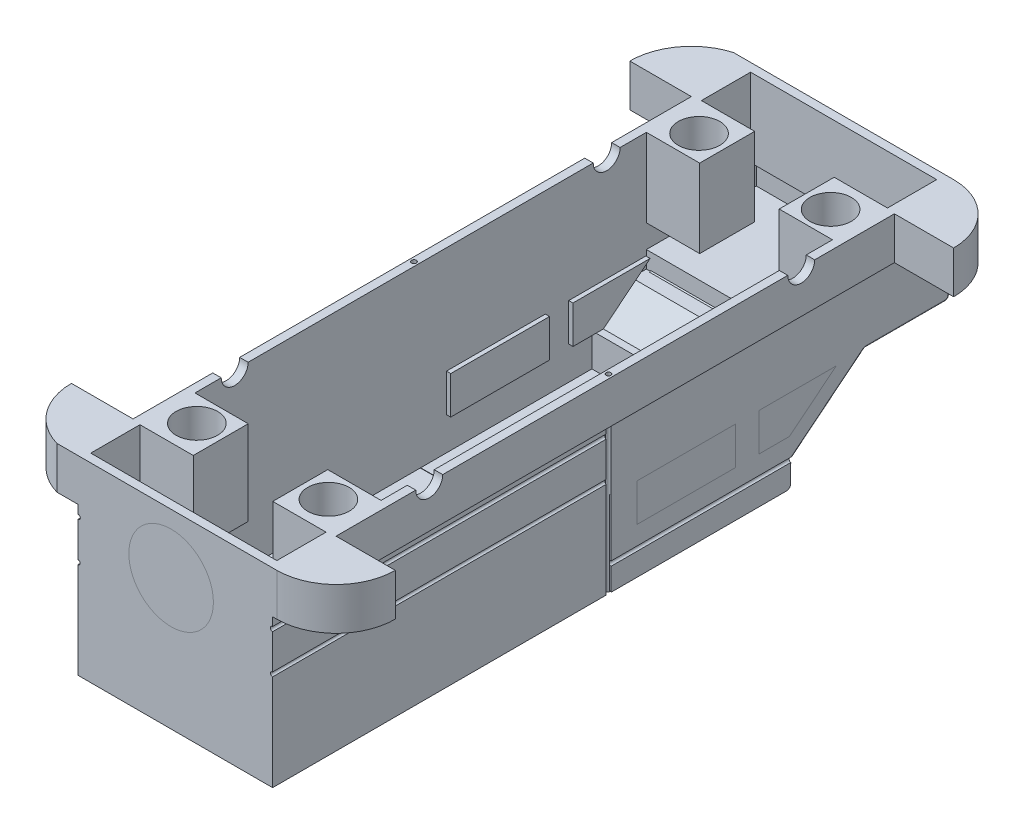
SolidWorks part; units mm, degrees
ref_plane "Front Plane" through (0, 0, 0) normal (0, 0, 1) x (1, 0, 0)
ref_plane "Top Plane" through (0, 0, 0) normal (0, 1, 0) x (1, 0, 0)
ref_plane "Right Plane" through (0, 0, 0) normal (1, 0, 0) x (0, 0, -1)
sketch "Sketch1" plane through (0, 0, 0) normal (0, 1, 0) x (1, 0, 0)
  line L1 (-24.8944, 17.78) -> (41.1456, 17.78)
  line L2 (-19.8144, 0) -> (-19.8144, -167.64)
  line L3 (-24.8944, -185.42) -> (41.1456, -185.42)
  line L4 (41.1456, 0) -> (41.1456, -167.64)
  line L5 (58.9256, 0) -> (41.1456, 0)
  line L6 (-38.3059, -167.64) -> (-19.8144, -167.64)
  line L7 (-38.3059, 0) -> (-19.8144, 0)
  line L8 (58.9256, -167.64) -> (41.1456, -167.64)
  arc A0 (58.9256, 0) -> (41.1456, 17.78) centre (41.1456, 0) ccw
  arc A1 (-38.3059, 0) -> (-24.8944, 17.78) centre (-19.8144, 0) cw
  arc A2 (-38.3059, -167.64) -> (-24.8944, -185.42) centre (-19.8144, -167.64) ccw
  arc A3 (58.9256, -167.64) -> (41.1456, -185.42) centre (41.1456, -167.64) cw
  dimension "D1" = 66.04
  dimension "D2" = 203.2
  dimension "D3" = 60.96
  dimension "0.8" = 17.78
extrude "Boss-Extrude1" add sketch "Sketch1" along normal blind 12.7 contours L1 A0 L5 L4 L8 A3 L3 A2 L6 L2 L7 A1
sketch "Sketch2" plane through (0, 12.7, 0) normal (0, 1, 0) x (1, 0, 0)
  line L0 (-19.8144, -27.94) -> (41.1456, -27.94)
  line L1 (-19.8144, 0) -> (-19.8144, -167.64) construction
  line L2 (41.1456, 0) -> (41.1456, -167.64) construction
  line L3 (58.9256, 0) -> (41.1456, 0) construction
  line L4 (-19.8144, -139.7) -> (41.1456, -139.7)
  line L6 (58.9256, -167.64) -> (41.1456, -167.64) construction
  dimension "D1" = 27.94
  dimension "D2" = 27.94
sketch "Sketch3" plane through (41.1456, 0, 0) normal (1, 0, 0) x (0, 0, -1)
  line L0 (0, 12.7) -> (-167.64, 12.7) construction
  circle A0 centre (-139.6638, 12.7) radius 4.0396
  circle A1 centre (-27.9739, 12.7) radius 4.0396
extrude "Cut-Extrude1" cut sketch "Sketch3" against normal through all
sketch "Sketch4" plane through (0, 12.7, 0) normal (0, 1, 0) x (1, 0, 0)
  line L0 (10.6656, 17.78) -> (10.6656, -185.42)
  line L1 (-24.8944, 17.78) -> (41.1456, 17.78) construction
  line L2 (-24.8944, -185.42) -> (41.1456, -185.42) construction
  line L3 (41.1456, -32.0134) -> (41.1456, -135.6242) construction
  circle A0 centre (30.4166, -8.428) radius 6.2278
  circle A2 centre (30.4166, -159.212) radius 6.2278
  circle A4 centre (-9.0854, -159.212) radius 6.2278
  circle A5 centre (-9.0854, -8.428) radius 6.2278
  dimension "D1" = 30.48
extrude "Cut-Extrude3" cut sketch "Sketch4" against normal blind 25.4 contours A5 | A0 | A4 | A2
ref_plane "Plane1" through (0, 0, 0) normal (0, -1, 0) x (-1, 0, 0)
sketch "Sketch5" plane through (0, 0, 0) normal (0, -1, 0) x (-1, 0, 0)
  line L0 (19.8144, 0) -> (19.8144, -167.64) construction
  line L1 (-39.8756, 17.78) -> (18.5444, 17.78)
  line L2 (-39.8756, 17.78) -> (-39.8756, -83.82)
  line L3 (-39.8756, -83.82) -> (18.5444, -83.82)
  line L4 (18.5444, 17.78) -> (18.5444, -83.82)
  line L5 (-41.1456, 0) -> (-41.1456, -167.64) construction
  line L6 (24.8944, 17.78) -> (-41.1456, 17.78) construction
  line L7 (24.8944, -185.42) -> (-41.1456, -185.42) construction
  line L8 (-39.8756, -83.82) -> (18.5444, -83.82)
  line L9 (-39.8756, -83.82) -> (-39.8756, -185.42)
  line L10 (-39.8756, -185.42) -> (18.5444, -185.42)
  line L11 (18.5444, -83.82) -> (18.5444, -185.42)
  dimension "D1" = 1.27
  dimension "D2" = 1.27
  dimension "D3" = 101.6
  dimension "0.0" = 0
extrude "Boss-Extrude2" add sketch "Sketch5" along normal blind 19.05 contours L4 L1 L2 L3
sketch "Sketch6" plane through (0, -19.05, 0) normal (0, -1, 0) x (1, 0, 0)
  line L0 (39.8756, -17.78) -> (39.8756, 83.82) construction
  line L1 (39.8756, 7.62) -> (-18.5444, 7.62)
  line L2 (39.8756, 7.62) -> (39.8756, 83.82)
  line L3 (39.8756, 83.82) -> (-18.5444, 83.82)
  line L4 (-18.5444, 7.62) -> (-18.5444, 83.82)
  line L5 (-18.5444, -17.78) -> (-18.5444, 83.82) construction
  line L6 (-18.5444, -17.78) -> (-18.5444, 83.82) construction
  line L7 (39.8756, -17.78) -> (-18.5444, -17.78) construction
  dimension "D1" = 25.4
  dimension "D2" = 76.2
extrude "Boss-Extrude3" add sketch "Sketch6" along normal blind 25.4
sketch "Sketch7" plane through (39.8756, 0, 0) normal (1, 0, 0) x (0, 0, -1)
  line L1 (-7.62, -19.05) -> (-29.8743, -36.9947)
  line L5 (-7.62, -44.45) -> (-7.62, -19.05) construction
  line L6 (17.78, -19.05) -> (-7.62, -19.05) construction
  line L7 (-29.8743, -36.9947) -> (-29.8743, -44.45)
  line L8 (-7.62, -44.45) -> (-83.82, -44.45) construction
  line L9 (-29.8743, -44.45) -> (-7.62, -44.45)
  line L10 (-7.62, -44.45) -> (-7.62, -19.05)
  dimension "D1" = 22.2543
fillet "Fillet1" radius 1.27 1 edges at (10.6656, -19.05, -17.78)
sketch "Sketch10" plane through (0, 0, 0) normal (0, -1, 0) x (-1, 0, 0)
  line L0 (24.8944, -185.42) -> (-41.1456, -185.42) construction
  line L1 (-39.8756, -83.82) -> (18.5444, -83.82)
  line L2 (-39.8756, -83.82) -> (-39.8756, -185.42)
  line L3 (-39.8756, -185.42) -> (18.5444, -185.42)
  line L4 (18.5444, -83.82) -> (18.5444, -185.42)
  line L5 (19.8144, 0) -> (19.8144, -167.64) construction
  dimension "D1" = 1.27
extrude "Boss-Extrude4" add sketch "Sketch10" along normal blind 19.05 contours L2 L1 L4 L3
sketch "Sketch11" plane through (0, -19.05, 0) normal (0, -1, 0) x (1, 0, 0)
  line L0 (39.8756, 83.82) -> (39.8756, 185.42) construction
  line L1 (-14.7344, 180.34) -> (36.0656, 180.34)
  line L2 (-14.7344, 180.34) -> (-14.7344, 88.9)
  line L3 (-14.7344, 88.9) -> (36.0656, 88.9)
  line L4 (36.0656, 180.34) -> (36.0656, 88.9)
  line L5 (-18.5444, 83.82) -> (-18.5444, 185.42) construction
  line L6 (-24.8944, 185.42) -> (41.1456, 185.42) construction
  line L7 (39.8756, 83.82) -> (-18.5444, 83.82) construction
  dimension "D1" = 3.81
  dimension "D2" = 3.81
  dimension "D3" = 5.08
  dimension "D4" = 5.08
extrude "Cut-Extrude5" cut sketch "Sketch11" against normal mid plane 12.7
ref_plane "Plane2" through (0, 12.7, 0) normal (0, 1, 0) x (1, 0, 0)
sketch "Sketch12" plane through (0, 12.7, 0) normal (0, 1, 0) x (1, 0, 0)
  line L0 (-19.8144, -32.0134) -> (-19.8144, -135.6242) construction
  line L1 (-17.2744, -16.048) -> (38.6056, -16.048)
  line L2 (-17.2744, -16.048) -> (-17.2744, -151.592)
  line L3 (-17.2744, -151.592) -> (38.6056, -151.592)
  line L4 (38.6056, -16.048) -> (38.6056, -151.592)
  line L5 (41.1456, -32.0134) -> (41.1456, -135.6242) construction
  circle A0 centre (-9.0854, -8.428) radius 6.2278 construction
  circle A1 centre (30.4166, -8.428) radius 6.2278 construction
  circle A2 centre (-9.0854, -159.212) radius 6.2278 construction
  dimension "D2" = 7.62
  dimension "D3" = 7.62
  dimension "D1" = 7.62
  dimension "D4" = 2.54
  dimension "D5" = 2.54
extrude "Cut-Extrude6" cut sketch "Sketch12" against normal blind 20.32
sketch "Sketch13" plane through (0, 12.7, 0) normal (0, 1, 0) x (1, 0, 0)
  line L0 (-24.8944, 17.78) -> (41.1456, 17.78) construction
  line L1 (-17.2744, 15.24) -> (38.6056, 15.24)
  line L2 (-17.2744, 15.24) -> (-17.2744, 0.462)
  line L3 (-17.2744, 0.462) -> (38.6056, 0.462)
  line L4 (38.6056, 15.24) -> (38.6056, 0.462)
  line L5 (-19.8144, 0) -> (-19.8144, -23.9343) construction
  line L6 (41.1456, 0) -> (41.1456, -23.9343) construction
  line L7 (-19.8144, -83.82) -> (41.1456, -83.82)
  line L8 (-19.8144, -32.0134) -> (-19.8144, -135.6242) construction
  line L9 (41.1456, -32.0134) -> (41.1456, -135.6242) construction
  line L10 (-17.2744, -168.102) -> (38.6056, -168.102)
  line L11 (38.6056, -182.88) -> (38.6056, -168.102)
  line L12 (-17.2744, -182.88) -> (38.6056, -182.88)
  line L13 (-17.2744, -182.88) -> (-17.2744, -168.102)
  circle A0 centre (-9.0854, -8.428) radius 6.2278 construction
  dimension "D1" = 2.54
  dimension "D2" = 2.54
  dimension "0.2" = 8.89
  dimension "0.1" = 2.54
  dimension "4" = 101.6
extrude "Cut-Extrude7" cut sketch "Sketch13" against normal mid plane 45.72 contours L4 L1 L2 L3 | L13 L12 L11 L10
extrude "Cut-Extrude8" cut sketch "Sketch7" against normal through all
sketch "Sketch14" plane through (0, -44.45, 0) normal (0, -1, 0) x (1, 0, 0)
  line L1 (-13.4644, 78.74) -> (34.7956, 78.74)
  line L2 (-13.4644, 78.74) -> (-13.4644, 34.9543)
  line L3 (-13.4644, 34.9543) -> (34.7956, 34.9543)
  line L4 (34.7956, 78.74) -> (34.7956, 34.9543)
  line L5 (-18.5444, 83.82) -> (-18.5444, 29.8743) construction
  line L6 (39.8756, 29.8743) -> (39.8756, 83.82) construction
  line L7 (39.8756, 29.8743) -> (-18.5444, 29.8743) construction
  line L8 (39.8756, 83.82) -> (-18.5444, 83.82) construction
  dimension "D1" = 5.08
  dimension "0.2" = 5.08
  dimension "D2" = 5.08
  dimension "D3" = 5.08
extrude "Cut-Extrude9" cut sketch "Sketch14" against normal mid plane 5.08
sketch "Sketch15" plane through (0, -7.62, 0) normal (0, 1, 0) x (1, 0, 0)
  line L0 (-17.2744, -32.0134) -> (-17.2744, -135.6242) construction
  line L1 (-17.2744, -16.048) -> (38.6056, -16.048)
  line L2 (-17.2744, -16.048) -> (-17.2744, -29.8743)
  line L3 (-17.2744, -29.8743) -> (38.6056, -29.8743)
  line L4 (38.6056, -16.048) -> (38.6056, -29.8743)
  line L5 (38.6056, -151.592) -> (38.6056, -16.048) construction
  line L8 (38.6056, -16.048) -> (-17.2744, -16.048) construction
  line L9 (-18.5444, -7.62) -> (39.8756, -7.62) construction
  line L12 (-18.5444, -29.8743) -> (-18.5444, -7.62) construction
  dimension "D1" = 0
  dimension "0.1" = 0
  dimension "0" = 0
  dimension "D2" = 22.2543
  dimension "D3" = 90
extrude "Cut-Extrude10" cut sketch "Sketch15" against normal blind 15.24
sketch "Sketch17" plane through (0, -7.62, 0) normal (0, 1, 0) x (1, 0, 0)
  line L0 (-17.2744, -29.8743) -> (-17.2744, -151.592) construction
  line L1 (-17.2744, -32.4143) -> (38.3008, -32.4143)
  line L2 (-17.2744, -32.4143) -> (-17.2744, -78.74)
  line L3 (-17.2744, -78.74) -> (38.3008, -78.74)
  line L4 (38.3008, -32.4143) -> (38.3008, -78.74)
  line L6 (-18.5444, -7.62) -> (39.8756, -7.62) construction
  line L7 (-17.2744, -29.8743) -> (38.6056, -29.8743) construction
  dimension "D1" = 71.12
  dimension "D2" = 2.54
extrude "Cut-Extrude12" cut sketch "Sketch17" against normal blind 33.02
sketch "Sketch20" plane through (0, -7.62, 0) normal (0, 1, 0) x (1, 0, 0)
  line L1 (-17.2744, -29.8743) -> (38.3008, -29.8743)
  line L2 (-17.2744, -29.8743) -> (-17.2744, -32.4143)
  line L3 (-17.2744, -32.4143) -> (38.3008, -32.4143)
  line L4 (38.3008, -29.8743) -> (38.3008, -32.4143)
extrude "Cut-Extrude13" cut sketch "Sketch20" against normal blind 15.24
sketch "Sketch21" plane through (39.8756, 0, 0) normal (1, 0, 0) x (0, 0, -1)
  line L0 (-30.2351, -30.7052) -> (-16.196, -19.3848)
  line L1 (-39.3632, -19.3848) -> (-16.196, -19.3848)
  line L2 (-30.2351, -30.7052) -> (-39.3632, -19.3848)
extrude "Cut-Extrude14" cut sketch "Sketch21" against normal blind 60.96
sketch "Sketch22" plane through (39.8756, 0, 0) normal (1, 0, 0) x (0, 0, -1)
  line L0 (-39.3632, -19.3848) -> (-39.3632, -30.7052)
  line L1 (-39.3632, -30.7052) -> (-30.2351, -30.7052)
  line L2 (-39.3632, -19.3848) -> (-30.2351, -30.7052)
extrude "Cut-Extrude15" cut sketch "Sketch22" against normal through all
sketch "Sketch25" plane through (0, -7.8207, -6.3062) normal (0, -0.7785, -0.6277) x (1, 0, 0)
  line L0 (-18.5444, 46.4774) -> (39.8756, 46.4774) construction
  line L1 (-16.0044, 43.9374) -> (37.3356, 43.9374)
  line L2 (-16.0044, 43.9374) -> (-16.0044, 20.4296)
  line L3 (-16.0044, 20.4296) -> (37.3356, 20.4296)
  line L4 (37.3356, 43.9374) -> (37.3356, 20.4296)
  line L5 (39.8756, 17.8896) -> (39.8756, 46.4774) construction
  line L6 (-18.5444, 46.4774) -> (-18.5444, 17.8896) construction
  line L7 (-18.5444, 17.8896) -> (39.8756, 17.8896) construction
  dimension "D1" = 2.54
  dimension "D2" = 2.54
  dimension "D3" = 2.54
  dimension "0.1" = 2.54
extrude "Boss-Extrude9" add sketch "Sketch25" against normal blind 2.54 separate body
sketch "Sketch26" plane through (-18.5444, 0, 0) normal (-1, 0, 0) x (0, 0, 1)
  line L0 (16.196, -19.3848) -> (39.3632, -19.3848)
  line L1 (39.3632, -19.3848) -> (39.3632, -30.7052)
  line L2 (39.3632, -30.7052) -> (30.2351, -30.7052)
  line L3 (30.2351, -30.7052) -> (16.196, -19.3848)
extrude "Boss-Extrude10" add sketch "Sketch26" against normal blind 2.54 separate body
sketch "Sketch27" plane through (39.8756, 0, 0) normal (1, 0, 0) x (0, 0, -1)
  line L0 (-39.3632, -19.3848) -> (-16.196, -19.3848)
  line L1 (-16.196, -19.3848) -> (-30.2351, -30.7052)
  line L2 (-30.2351, -30.7052) -> (-39.3632, -30.7052)
  line L3 (-39.3632, -30.7052) -> (-39.3632, -19.3848)
extrude "Boss-Extrude11" add sketch "Sketch27" against normal blind 2.54 separate body contours L3 L0 L1 L2
sketch "Sketch28" plane through (0, -44.45, 0) normal (0, -1, 0) x (1, 0, 0)
  line L0 (39.8756, 29.8743) -> (39.8756, 83.82) construction
  line L1 (10.6656, 83.82) -> (10.6656, 27.94)
  line L2 (39.8756, 83.82) -> (-18.5444, 83.82) construction
  line L3 (-19.8144, 27.94) -> (41.1456, 27.94) construction
  circle A0 centre (39.8756, 42.6587) radius 0.5895
  circle A1 centre (-18.5444, 42.6587) radius 0.5895
  dimension "D1" = 29.21
sketch "Sketch29" plane through (39.8756, 0, 0) normal (1, 0, 0) x (0, 0, -1)
  line L0 (-16.196, -19.3848) -> (-39.3632, -19.3848) construction
  line L1 (-76.0738, -19.3848) -> (-46.4134, -19.3848)
  line L2 (-76.0738, -19.3848) -> (-76.0738, -30.7052)
  line L3 (-76.0738, -30.7052) -> (-46.4134, -30.7052)
  line L4 (-46.4134, -19.3848) -> (-46.4134, -30.7052)
  line L5 (-30.2351, -30.7052) -> (-39.3632, -30.7052) construction
  dimension "D1" = 0
  dimension "D2" = 0
sketch "Sketch30" plane through (0, 0, 185.42) normal (0, 0, 1) x (1, 0, 0)
  line L0 (39.8756, -19.05) -> (39.8756, 0) construction
  line L1 (39.8756, 12.7) -> (39.8756, -19.05)
  line L5 (-19.8144, 12.7) -> (41.1456, 12.7) construction
  line L8 (39.8756, -19.05) -> (-18.5444, -19.05) construction
  line L9 (10.6656, 12.7) -> (10.6656, -19.05)
  line L10 (39.8756, -19.05) -> (-18.5444, -19.05) construction
  circle A0 centre (39.8756, -14.9961) radius 0.6347
  circle A1 centre (39.8756, -3.2183) radius 0.6699
  circle A2 centre (-18.5444, -14.9961) radius 0.6347
  circle A3 centre (-18.5444, -3.2183) radius 0.6699
  dimension "D1" = 0
  dimension "D2" = 29.21
sketch "Sketch33" plane through (0, -19.05, 0) normal (0, -1, 0) x (1, 0, 0)
  line L1 (39.8756, 83.82) -> (39.8756, 185.42) construction
  line L2 (10.6656, 185.42) -> (10.6656, 84.582)
  line L3 (39.8756, 185.42) -> (-18.5444, 185.42) construction
  line L4 (41.1456, 0) -> (41.1456, 167.64) construction
  circle A0 centre (39.8756, 84.582) radius 0.7046
  circle A1 centre (-18.5444, 84.582) radius 0.7046
  dimension "D1" = 0.762
  dimension "D2" = 30.48
sketch "Sketch34" plane through (0, 0, 83.82) normal (0, 0, 1) x (1, 0, 0)
  line L0 (39.8756, -44.45) -> (39.8756, -19.05) construction
  line L1 (-18.5444, -36.9947) -> (39.8756, -36.9947) construction
  line L2 (10.6656, -19.05) -> (10.6656, -44.45)
  line L6 (39.8756, -19.05) -> (-18.5444, -19.05) construction
  line L7 (39.8756, -44.45) -> (-18.5444, -44.45) construction
  circle A0 centre (39.8756, -36.9947) radius 0.683
  circle A1 centre (-18.5444, -36.9947) radius 0.683
  dimension "D1" = 0
  dimension "D2" = 29.21
extrude "Cut-Extrude22" cut sketch "Sketch30" against normal mid plane 200.66 contours A0 | A1 | A2 | A3
extrude "Cut-Extrude23" cut sketch "Sketch33" against normal through all both and the other way through all contours A1 | A0
extrude "Cut-Extrude24" cut sketch "Sketch34" against normal blind 200.66 contours A1 | A0
extrude "Cut-Extrude25" cut sketch "Sketch29" against normal through all
sketch "Sketch38" plane through (39.8756, 0, 0) normal (1, 0, 0) x (0, 0, -1)
  line L0 (-76.0738, -19.3848) -> (-46.4134, -19.3848)
  line L1 (-46.4134, -19.3848) -> (-46.4134, -30.7052)
  line L2 (-46.4134, -30.7052) -> (-76.0738, -30.7052)
  line L3 (-76.0738, -30.7052) -> (-76.0738, -19.3848)
extrude "Boss-Extrude13" add sketch "Sketch38" against normal blind 2.54 separate body contours L3 L0 L1 L2
sketch "Sketch39" plane through (-18.5444, 0, 0) normal (-1, 0, 0) x (0, 0, 1)
  line L0 (46.4134, -19.3848) -> (76.0738, -19.3848)
  line L1 (76.0738, -19.3848) -> (76.0738, -30.7052)
  line L2 (76.0738, -30.7052) -> (46.4134, -30.7052)
  line L3 (46.4134, -30.7052) -> (46.4134, -19.3848)
extrude "Boss-Extrude14" add sketch "Sketch39" against normal blind 2.54 separate body
fillet "Fillet2" radius 2.54 1 edges at (10.6656, -36.9947, 29.8743)
fillet "Fillet4" radius 0.254 1 edges at (10.6656, -44.45, 83.82)
fillet "Fillet5" radius 1.27 1 edges at (10.6656, -44.45, 29.8743)
fillet "Fillet6" radius 1.27 1 edges at (10.6656, -19.05, 7.62)
extrude "Cut-Extrude26" [suppressed] cut sketch "Sketch28" against normal through all contours A0 | A1
sketch "Sketch42" [suppressed] plane through (0, -19.05, 0) normal (0, -1, 0) x (1, 0, 0)
  line L0 (39.8756, -16.51) -> (39.8756, 7.1718) construction
  line L1 (10.6656, 34.9543) -> (10.6656, -16.51)
  line L2 (-13.4644, 34.9543) -> (34.7956, 34.9543) construction
  line L3 (-18.5444, -16.51) -> (39.8756, -16.51) construction
  circle A0 centre (39.8756, 6.842) radius 0.7453
  circle A1 centre (-18.5444, 6.842) radius 0.7453
extrude "Cut-Extrude28" [suppressed] cut sketch "Sketch42" against normal through all contours A1 | A0
sketch "Sketch43" plane through (0, 0, -17.78) normal (0, 0, -1) x (-1, 0, 0)
  line L0 (19.8144, 12.7) -> (-41.1456, 12.7) construction
  line L1 (-37.3356, 10.16) -> (-27.074, 10.16)
  line L2 (-37.3356, 10.16) -> (-37.3356, -15.24)
  line L3 (-37.3356, -15.24) -> (-27.074, -15.24)
  line L6 (-39.8756, -17.78) -> (18.5444, -17.78) construction
  line L7 (-39.8756, -17.78) -> (-39.8756, 0) construction
  line L8 (-27.074, 10.16) -> (-27.074, -15.24)
  line L9 (-12.596, 10.16) -> (-12.596, -15.24)
  line L10 (-22.8576, -15.24) -> (-12.596, -15.24)
  line L11 (-22.8576, 10.16) -> (-22.8576, -15.24)
  line L12 (-22.8576, 10.16) -> (-12.596, 10.16)
  line L13 (1.882, 10.16) -> (1.882, -15.24)
  line L14 (-8.3796, -15.24) -> (1.882, -15.24)
  line L15 (-8.3796, 10.16) -> (-8.3796, -15.24)
  line L16 (-8.3796, 10.16) -> (1.882, 10.16)
  line L17 (16.36, 10.16) -> (16.36, -15.24)
  line L18 (6.0984, -15.24) -> (16.36, -15.24)
  line L19 (6.0984, 10.16) -> (6.0984, -15.24)
  line L20 (6.0984, 10.16) -> (16.36, 10.16)
  dimension "D1" = 2.54
  dimension "D2" = 4
  dimension "D3" = 2.54
  dimension "D4" = 2.54
extrude "Cut-Extrude30" cut sketch "Sketch43" against normal blind 0.508 contours L9 L10 L11 L12 | L13 L14 L15 L16 | L17 L18 L19 L20 | L8 L3 L2 L1
fillet "Fillet7" radius 0.508 6 edges at (39.8756, -8.89, -17.78) (39.8756, -18.678, -17.408) (39.8756, -36.2714, 28.9761) (39.8756, -27.7818, 18.4488) (39.8756, -19.1224, 7.5944) (39.8756, -19.05, -4.6691)
fillet "Fillet8" radius 0.508 6 edges at (-18.5444, -8.89, -17.78) (-18.5444, -18.678, -17.408) (-18.5444, -36.2714, 28.9761) (-18.5444, -27.7818, 18.4488) (-18.5444, -19.1224, 7.5944) (-18.5444, -19.05, -4.6691)
sketch "Sketch45" plane through (0, -19.05, 0) normal (0, -1, 0) x (-1, 0, 0)
  line L0 (17.9097, -185.42) -> (-39.8756, -185.42)
  line L1 (-39.8756, -185.42) -> (-39.8756, -84.582)
  line L3 (18.5444, -185.42) -> (-39.8756, -185.42)
  line L4 (18.5444, -185.42) -> (18.5444, -83.9348)
  line L5 (18.5444, -83.9348) -> (-39.8756, -83.9348)
  line L6 (-39.8756, -185.42) -> (-39.8756, -83.9348)
  line M1 (-36.0656, -88.9) -> (14.7344, -88.9)
  line M2 (14.7344, -88.9) -> (14.7344, -180.34)
  line M3 (14.7344, -180.34) -> (-36.0656, -180.34)
  line M4 (-36.0656, -180.34) -> (-36.0656, -88.9)
  arc M5 (18.5444, -85.2866) -> (18.5444, -83.8774) centre (18.5444, -84.582) cw
  arc M9 (-39.8756, -83.8774) -> (-39.8756, -85.2866) centre (-39.8756, -84.582) cw
  line M10 (-39.8756, -85.2866) -> (-39.8756, -185.42)
  line M11 (-39.8756, -185.42) -> (18.5444, -185.42)
  line M12 (18.5444, -185.42) -> (18.5444, -85.2866)
extrude "Boss-Extrude15" add sketch "Sketch45" along normal blind 25.4 contours L5 M5 M9 M10 M11 M12 M4 M1 M2 M3
sketch "Sketch46" plane through (0, -44.45, 0) normal (0, -1, 0) x (1, 0, 0)
  line L0 (39.8756, 185.42) -> (-18.5444, 185.42) construction
  line L1 (-14.7344, 181.61) -> (36.0656, 181.61)
  line L2 (-14.7344, 181.61) -> (-14.7344, 87.7448)
  line L3 (-14.7344, 87.7448) -> (36.0656, 87.7448)
  line L4 (36.0656, 181.61) -> (36.0656, 87.7448)
  line L5 (39.8756, 83.9348) -> (39.8756, 185.42) construction
  line L6 (-18.5444, 185.42) -> (-18.5444, 83.9348) construction
  line L7 (-18.5444, 83.9348) -> (39.8756, 83.9348) construction
  dimension "D1" = 3.81
  dimension "D2" = 3.81
  dimension "D3" = 3.81
  dimension "D4" = 3.81
  dimension "D5" = 3.81
extrude "Cut-Extrude31" cut sketch "Sketch46" against normal blind 2.54
sketch "Sketch47" plane through (0, -44.45, 0) normal (0, -1, 0) x (-1, 0, 0)
  line L0 (18.5444, -185.42) -> (18.5444, -83.9348) construction
  circle A0 centre (-39.8756, -84.582) radius 0.7046
  circle A1 centre (18.5444, -84.582) radius 0.7368
extrude "Cut-Extrude32" cut sketch "Sketch47" against normal through all
sketch "Sketch49" plane through (0, -7.62, 0) normal (0, 1, 0) x (1, 0, 0)
  line L1 (-17.2744, -78.74) -> (38.6056, -78.74)
  line L2 (-17.2744, -78.74) -> (-17.2744, -151.592)
  line L3 (-17.2744, -151.592) -> (38.6056, -151.592)
  line L4 (38.6056, -78.74) -> (38.6056, -151.592)
extrude "Cut-Extrude33" cut sketch "Sketch49" against normal blind 33.02
sketch "Sketch50" plane through (0, 0, 151.592) normal (0, 0, -1) x (-1, 0, 0)
  line L0 (-36.0656, -12.7) -> (14.7344, -12.7) construction
  line L1 (-22.6036, 12.7) -> (1.2724, 12.7)
  line L2 (-22.6036, 12.7) -> (-22.6036, -4.6278)
  line L3 (-22.6036, -4.6278) -> (1.2724, -4.6278)
  line L4 (1.2724, 12.7) -> (1.2724, -4.6278)
  line L5 (1.2724, -4.6278) -> (-22.6036, -4.6278)
  line L6 (1.2724, -4.6278) -> (1.2724, -12.7)
  line L7 (1.2724, -12.7) -> (-22.6036, -12.7)
  line L8 (-22.6036, -4.6278) -> (-22.6036, -12.7)
  line L9 (17.2744, 12.7) -> (-38.6056, 12.7) construction
  line L13 (17.2744, -40.64) -> (17.2744, 12.7) construction
  line L15 (-38.6056, -40.64) -> (-38.6056, 12.7) construction
  line M9 (17.2744, 12.7) -> (-38.6056, 12.7)
  line M13 (-36.0656, -12.7) -> (14.7344, -12.7)
  dimension "D1" = 0
  dimension "D2" = 180
  dimension "D3" = 16.002
  dimension "D4" = 16.002
extrude "Cut-Extrude34" cut sketch "Sketch50" against normal blind 30.48 contours L4 L2 L3 M9 | L3 L8 L6 M13
sketch "Sketch51" plane through (0, -19.05, 0) normal (0, 1, 0) x (1, 0, 0)
  line L0 (-17.2744, -151.592) -> (38.6056, -151.592) construction
  line L1 (-14.6263, -151.592) -> (37.6736, -151.592)
  line L2 (-14.6263, -151.592) -> (-14.6263, -182.88)
  line L3 (-14.6263, -182.88) -> (37.6736, -182.88)
  line L4 (37.6736, -151.592) -> (37.6736, -182.88)
  line L5 (-17.2744, -182.88) -> (38.6056, -182.88) construction
sketch "Sketch53" plane through (0, -19.05, 0) normal (0, 1, 0) x (1, 0, 0)
  line L1 (-14.6263, -151.592) -> (37.6736, -151.592)
  line L2 (-14.6263, -151.592) -> (-14.6263, -182.88)
  line L3 (-14.6263, -182.88) -> (37.6736, -182.88)
  line L4 (37.6736, -151.592) -> (37.6736, -182.88)
extrude "Cut-Extrude37" cut sketch "Sketch53" against normal blind 21.59
sketch "Sketch54" plane through (0, 0, -0.462) normal (0, 0, -1) x (-1, 0, 0)
  line L5 (17.2744, -10.16) -> (-38.6056, -10.16) construction
  line L6 (-22.6036, 12.7) -> (1.2724, 12.7)
  line L7 (-22.6036, 12.7) -> (-22.6036, -10.16)
  line L8 (-22.6036, -10.16) -> (1.2724, -10.16)
  line L9 (1.2724, 12.7) -> (1.2724, -10.16)
  line L10 (-38.6056, 12.7) -> (17.2744, 12.7) construction
  line L11 (17.2744, -10.16) -> (17.2744, 12.7) construction
  line L12 (-38.6056, -10.16) -> (-38.6056, 12.7) construction
  dimension "D1" = 0
  dimension "D2" = 0
  dimension "D3" = 16.002
  dimension "D4" = 16.002
extrude "Cut-Extrude38" cut sketch "Sketch54" against normal blind 20.32
sketch "Sketch55" plane through (0, -10.16, 0) normal (0, 1, 0) x (1, 0, 0)
  line L0 (38.6056, -182.88) -> (38.6056, -168.102) construction
  line L1 (-17.2744, -168.102) -> (38.6056, -168.102)
  line L2 (-17.2744, -168.102) -> (-17.2744, -182.88)
  line L3 (-17.2744, -182.88) -> (38.6056, -182.88)
  line L4 (38.6056, -168.102) -> (38.6056, -182.88)
  line L5 (-17.2744, -182.88) -> (38.6056, -182.88) construction
extrude "Cut-Extrude39" cut sketch "Sketch55" against normal blind 30.48
sketch "Sketch56" plane through (0, 0, 16.048) normal (0, 0, 1) x (1, 0, 0)
  line L0 (38.6056, -22.86) -> (38.6056, 12.7) construction
  line L1 (-17.2744, -10.8376) -> (38.6056, -10.8376)
  line L2 (-17.2744, -10.8376) -> (-17.2744, -17.78)
  line L3 (-17.2744, -17.78) -> (38.6056, -17.78)
  line L4 (38.6056, -10.8376) -> (38.6056, -17.78)
  line L5 (-17.2744, -22.86) -> (-17.2744, 12.7) construction
  line L6 (38.6056, 12.7) -> (22.6036, 12.7) construction
  dimension "D1" = 0
  dimension "D2" = 0
  dimension "D3" = 30.48
extrude "Cut-Extrude40" cut sketch "Sketch56" against normal blind 33.02
sketch "Sketch57" plane through (0, -10.16, 0) normal (0, 1, 0) x (1, 0, 0)
  line L1 (-17.2744, 15.24) -> (38.6056, 15.24)
  line L2 (-17.2744, 15.24) -> (-17.2744, 0.462)
  line L3 (-17.2744, 0.462) -> (38.6056, 0.462)
  line L4 (38.6056, 15.24) -> (38.6056, 0.462)
extrude "Cut-Extrude41" cut sketch "Sketch57" against normal blind 5.08
sketch "Sketch58" plane through (0, -10.16, 0) normal (0, 1, 0) x (1, 0, 0)
  line L1 (-1.2724, 0.462) -> (22.6036, 0.462)
  line L2 (-1.2724, 0.462) -> (-1.2724, -16.048)
  line L3 (-1.2724, -16.048) -> (22.6036, -16.048)
  line L4 (22.6036, 0.462) -> (22.6036, -16.048)
extrude "Cut-Extrude42" cut sketch "Sketch58" against normal blind 5.08
sketch "Sketch59" plane through (0, 0, 185.42) normal (0, 0, 1) x (1, 0, 0)
  line L1 (39.8756, -14.3614) -> (39.8756, -3.8882) construction
  circle A2 centre (9.3956, -5.1466) radius 12.7
  dimension ".1" = 30.48
extrude "Cut-Extrude43" cut sketch "Sketch59" against normal blind 2.54 contours A2
sketch "Sketch60" plane through (0, 0, 185.42) normal (0, 0, 1) x (1, 0, 0)
  circle A0 centre (9.3956, -5.1466) radius 12.7
extrude "Boss-Extrude17" add sketch "Sketch60" against normal blind 2.54 separate body
sketch "Sketch62" plane through (0, -44.45, 0) normal (0, -1, 0) x (1, 0, 0)
  line L1 (-18.5444, 185.42) -> (39.8756, 185.42)
  line L2 (-18.5444, 185.42) -> (-18.5444, 83.82)
  line L3 (-18.5444, 83.82) -> (39.8756, 83.82)
  line L4 (39.8756, 185.42) -> (39.8756, 83.82)
